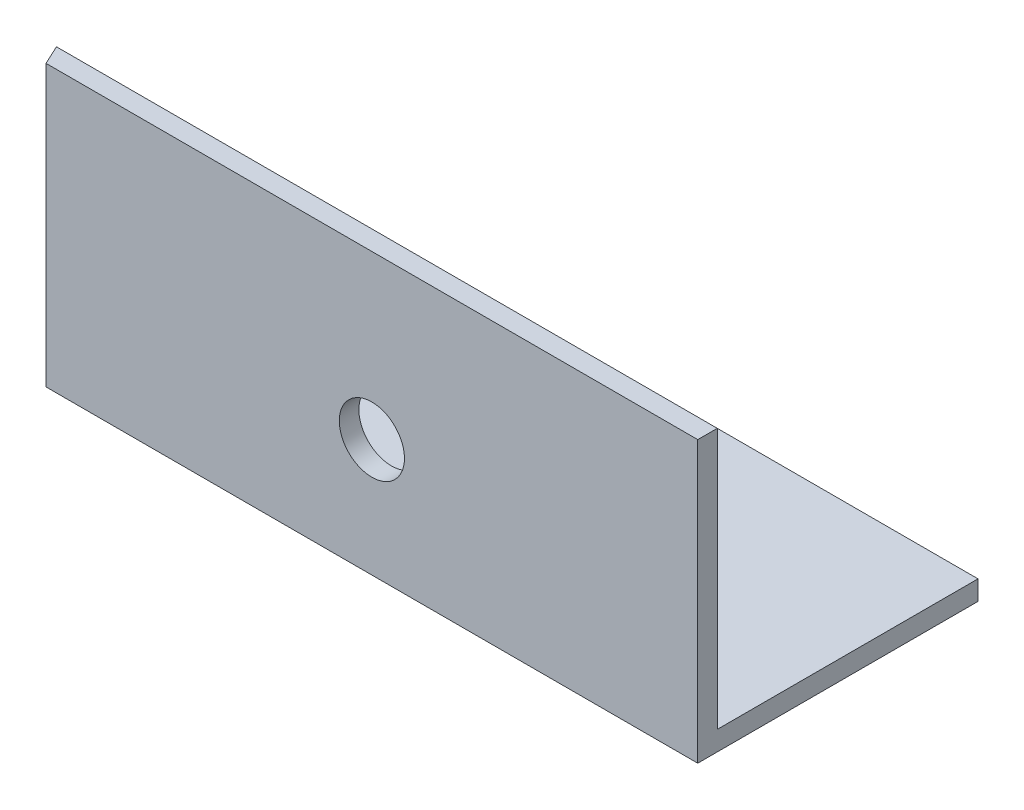
SolidWorks part; units mm, degrees
ref_plane "Спереди" through (0, 0, 0) normal (0, 0, 1) x (1, 0, 0)
ref_plane "Сверху" through (0, 0, 0) normal (0, 1, 0) x (1, 0, 0)
ref_plane "Справа" through (0, 0, 0) normal (1, 0, 0) x (0, 0, -1)
sketch "Эскиз1" plane through (0, 0, 0) normal (1, 0, 0) x (0, 0, -1)
  line L0 (0, 40) -> (0, 0)
  line L1 (0, 0) -> (40, 0)
extrude "Вытянуть-Тонкостенный1" add sketch "Эскиз1" along normal blind 120 thin
sketch "Эскиз2" plane through (0, -3, 0) normal (0, 1, 0) x (1, 0, 0)
  line L0 (0, 40) -> (20, -3)
  line L2 (20, -3) -> (0, -3)
  line L3 (0, -3) -> (0, 40)
  line L4 (120, 40) -> (0, 40) construction
  line L5 (120, -3) -> (0, -3) construction
extrude "Вырез-Вытянуть1" cut sketch "Эскиз2" along normal blind 50
sketch "Эскиз3" plane through (0, 0, 3) normal (0, 0, 1) x (1, 0, 0)
  circle A0 centre (70, 15) radius 5
extrude "Вырез-Вытянуть2" cut sketch "Эскиз3" against normal blind 10
